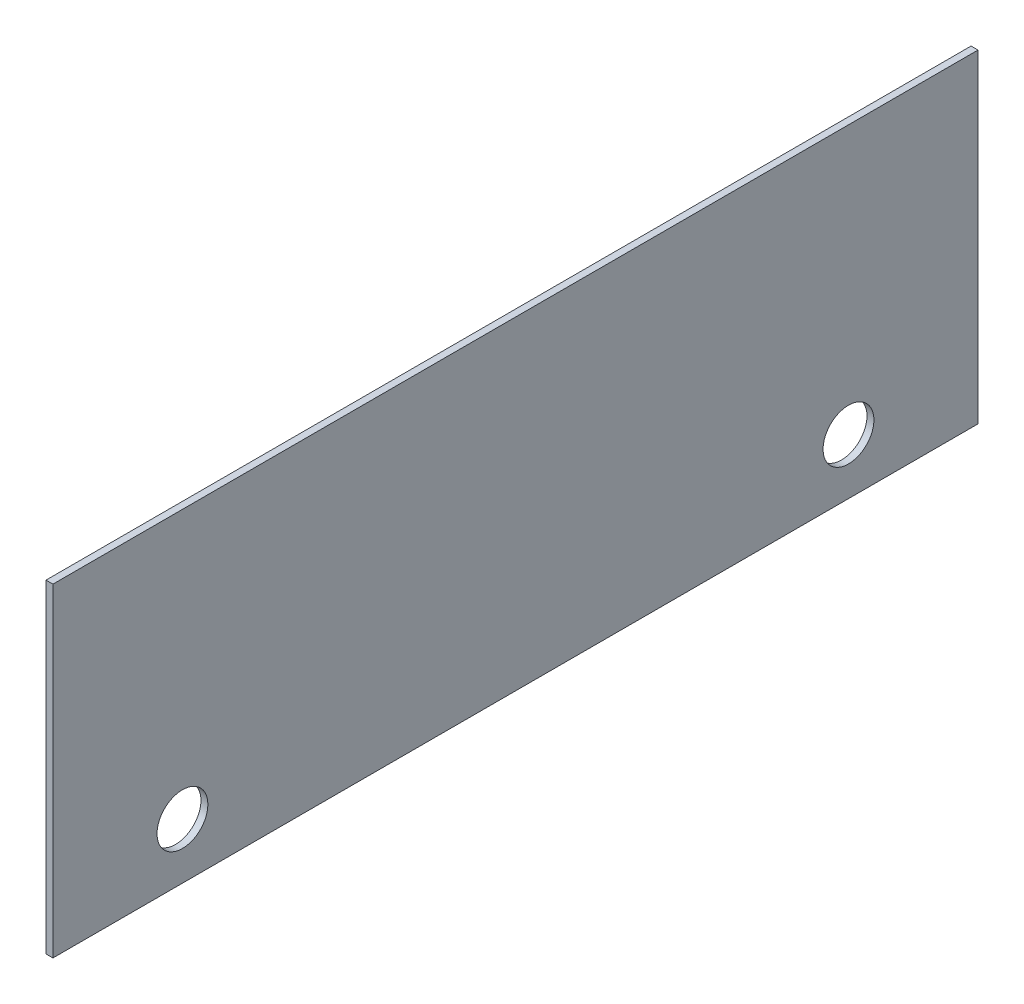
SolidWorks part; units mm, degrees
ref_plane "Front Plane" through (0, 0, 0) normal (0, 0, 1) x (1, 0, 0)
ref_plane "Top Plane" through (0, 0, 0) normal (0, 1, 0) x (1, 0, 0)
ref_plane "Right Plane" through (0, 0, 0) normal (1, 0, 0) x (0, 0, -1)
sketch "Sketch1" plane through (0, 0, 0) normal (0, 0, 1) x (1, 0, 0)
  line L1 (0, 0) -> (4.7625, 0)
  line L2 (0, 0) -> (0, 222.25)
  line L3 (0, 222.25) -> (4.7625, 222.25)
  line L4 (4.7625, 0) -> (4.7625, 222.25)
  dimension "D1" = 4.7625
  dimension "D2" = 222.25
extrude "Boss-Extrude1" add sketch "Sketch1" along normal blind 635
sketch "Sketch2" plane through (4.7625, 0, 0) normal (1, 0, 0) x (0, 0, -1)
  line L0 (-635, 0) -> (0, 0) construction
  line L1 (0, 0) -> (0, 222.25) construction
  line L2 (-635, 0) -> (-635, 222.25) construction
  circle A0 centre (-546.1, 38.1) radius 17.45
  circle A1 centre (-88.9, 38.1) radius 17.45
  dimension "D5" = 34.9
  dimension "D6" = 34.9
  dimension "D1" = 38.1
  dimension "D2" = 38.1
  dimension "D3" = 88.9
  dimension "D4" = 88.9
extrude "Cut-Extrude1" cut sketch "Sketch2" against normal through all
